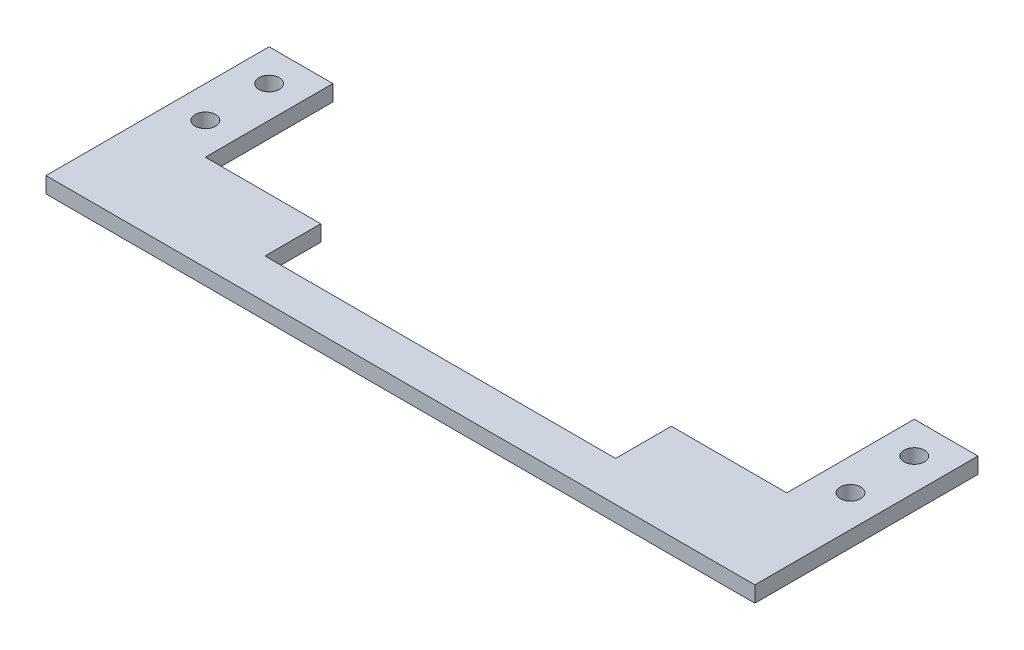
SolidWorks part; units mm, degrees
material "Polyethylene Cross-Linked"
ref_plane "Front Plane" through (0, 0, 0) normal (0, 0, 1) x (1, 0, 0)
ref_plane "Top Plane" through (0, 0, 0) normal (0, 1, 0) x (1, 0, 0)
ref_plane "Right Plane" through (0, 0, 0) normal (1, 0, 0) x (0, 0, -1)
sketch "Sketch1" plane through (0, 0, 0) normal (0, 1, 0) x (1, 0, 0)
  line L0 (0, 44.45) -> (12.7, 44.45)
  line L1 (0, 0) -> (141.224, 0)
  line L2 (0, 0) -> (0, 44.45)
  line L4 (141.224, 0) -> (141.224, 44.45)
  line L5 (141.224, 44.45) -> (128.524, 44.45)
  line L6 (12.7, 44.45) -> (12.7, 19.05)
  line L8 (128.524, 19.05) -> (128.524, 44.45)
  line L9 (12.7, 19.05) -> (35.687, 19.05)
  line L10 (105.537, 19.05) -> (128.524, 19.05)
  line L12 (35.687, 19.05) -> (35.687, 7.9375)
  line L13 (35.687, 7.9375) -> (105.537, 7.9375)
  line L14 (105.537, 19.05) -> (105.537, 7.9375)
  line L15 (0, 44.45) -> (0, 19.05)
  circle A0 centre (6.35, 38.1) radius 2.032
  circle A1 centre (6.35, 25.4) radius 2.032
  circle A2 centre (134.874, 38.1) radius 2.032
  circle A3 centre (134.874, 25.4) radius 2.032
  point P12 (70.612, 19.05)
extrude "Boss-Extrude1" add sketch "Sketch1" along normal blind 3.175 contours L10 L14 L13 L12 L9 L6 L0 L2 L1 L4 L5 L8 A2 A1 A0 A3
